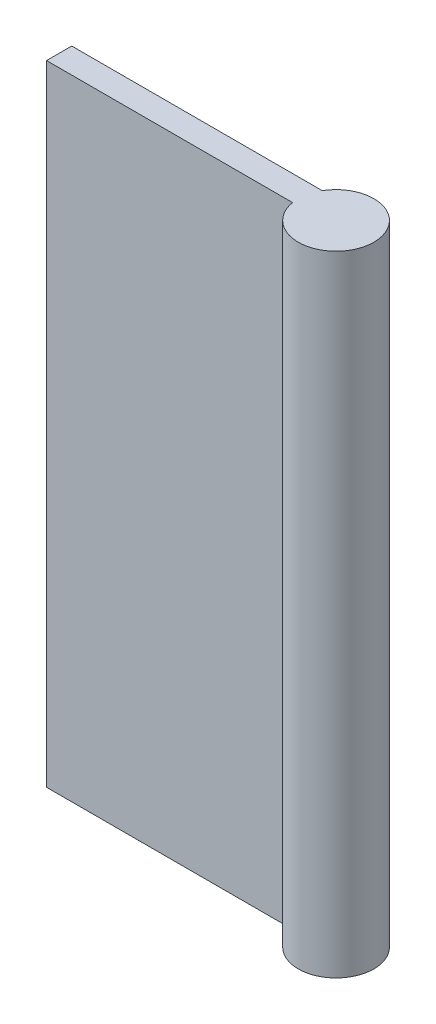
SolidWorks part; units mm, degrees
material "Stainless Steel (ferritic)"
ref_plane "Front Plane" through (0, 0, 0) normal (0, 0, 1) x (1, 0, 0)
ref_plane "Top Plane" through (0, 0, 0) normal (0, 1, 0) x (1, 0, 0)
ref_plane "Right Plane" through (0, 0, 0) normal (1, 0, 0) x (0, 0, -1)
sketch "Sketch1" plane through (0, 0, 0) normal (0, 0, 1) x (1, 0, 0)
  line L1 (-10, -25) -> (10, -25)
  line L2 (-10, -25) -> (-10, 25)
  line L3 (-10, 25) -> (10, 25)
  line L4 (10, -25) -> (10, 25)
  line L5 (-10, -25) -> (10, 25) construction
  line L6 (-10, 25) -> (10, -25) construction
  point P0 (0, 0)
  dimension "D1" = 20
  dimension "D2" = 50
extrude "Boss-Extrude1" add sketch "Sketch1" along normal blind 2
sketch "Sketch2" plane through (0, 25, 0) normal (0, 1, 0) x (1, 0, 0)
  line L0 (10, -2) -> (10, 0) construction
  circle A0 centre (12.5, -1.5) radius 3
  dimension "D1" = 6
  dimension "D2" = 2.5
extrude "Boss-Extrude2" add sketch "Sketch2" against normal blind 50
